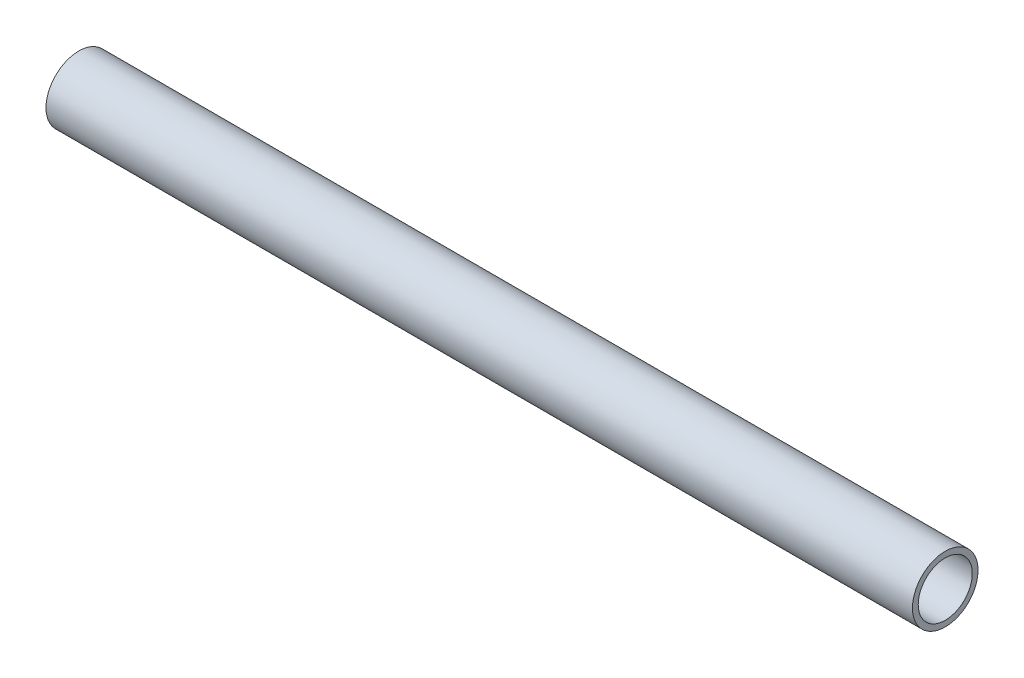
SolidWorks part; units mm, degrees
ref_plane "Front Plane" through (0, 0, 0) normal (0, 0, 1) x (1, 0, 0)
ref_plane "Top Plane" through (0, 0, 0) normal (0, 1, 0) x (1, 0, 0)
ref_plane "Right Plane" through (0, 0, 0) normal (1, 0, 0) x (0, 0, -1)
sketch "Sketch2" plane through (0, 0, 0) normal (0, 0, 1) x (1, 0, 0)
  line L0 (-90.9007, 684.2806) -> (-174.757, 684.2806)
other "Pipe 0.5 SCH 40(1)"
ref_plane "Plane1" through (-90.9007, 684.2806, 0) normal (-1, 0, 0) x (0, -1, 0)
sketch "Sketch1" plane through (-90.9007, 684.2806, 0) normal (-1, 0, 0) x (0, -1, 0)
  circle A0 centre (0, 0) radius 2.6162
  circle A1 centre (0, 0) radius 3.175
  point P5 (0, 0)
  dimension "In_dia" = 5.2324
  dimension "Out_dia" = 6.35
